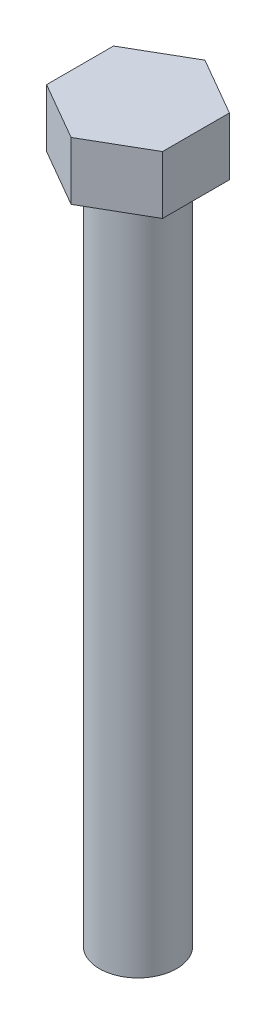
SolidWorks part; units mm, degrees
ref_plane "Спереди" through (0, 0, 0) normal (0, 0, 1) x (1, 0, 0)
ref_plane "Сверху" through (0, 0, 0) normal (0, 1, 0) x (1, 0, 0)
ref_plane "Справа" through (0, 0, 0) normal (1, 0, 0) x (0, 0, -1)
sketch "Эскиз1" plane through (0, 0, 0) normal (0, 1, 0) x (1, 0, 0)
  line L1 (0, -6.9282) -> (6, -3.4641)
  line L2 (6, -3.4641) -> (6, 3.4641)
  line L3 (6, 3.4641) -> (0, 6.9282)
  line L4 (0, 6.9282) -> (-6, 3.4641)
  line L5 (-6, 3.4641) -> (-6, -3.4641)
  line L6 (-6, -3.4641) -> (0, -6.9282)
  circle A0 centre (0, 0) radius 6 construction
extrude "Бобышка-Вытянуть1" add sketch "Эскиз1" along normal blind 6
sketch "Эскиз2" plane through (0, 0, 0) normal (0, -1, 0) x (1, 0, 0)
  circle A0 centre (0, 0) radius 4
extrude "Бобышка-Вытянуть2" add sketch "Эскиз2" along normal blind 70
